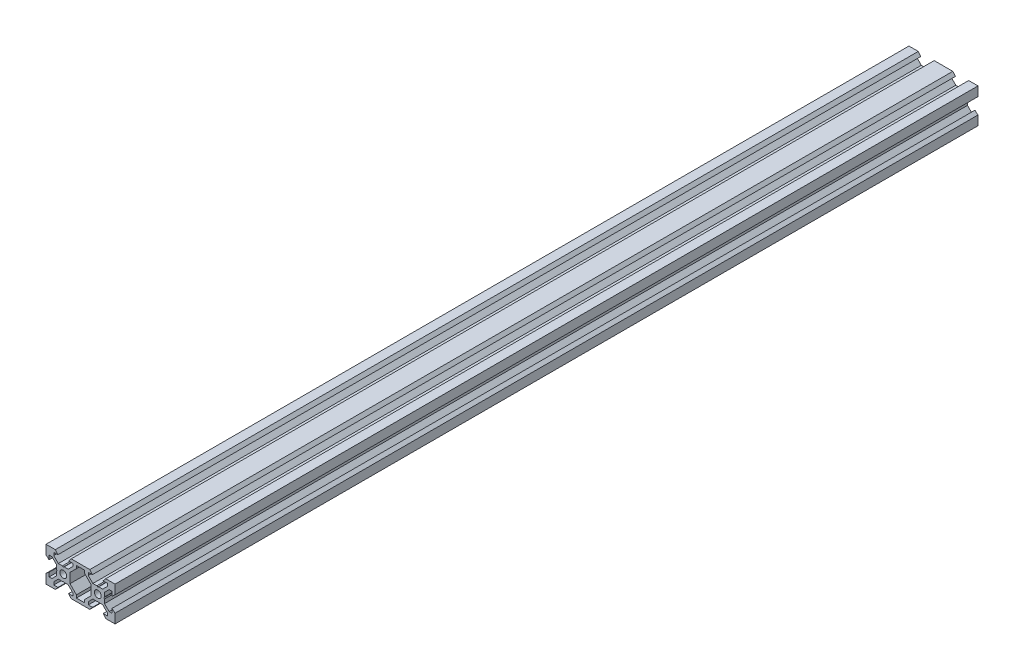
SolidWorks part; units mm, degrees
ref_plane "Front Plane" through (0, 0, 0) normal (0, 0, 1) x (1, 0, 0)
ref_plane "Top Plane" through (0, 0, 0) normal (0, 1, 0) x (1, 0, 0)
ref_plane "Right Plane" through (0, 0, 0) normal (1, 0, 0) x (0, 0, -1)
sketch "Sketch1" plane through (0, 0, 0) normal (0, 0, 1) x (1, 0, 0)
  line L0 (-5.3896, 10) -> (5.3896, 10)
  line L1 (0, 10) -> (0, 4.6104) construction
  line L2 (-6.1, -2.8393) -> (-2.3769, -6.5562)
  line L3 (5.3896, -10) -> (-5.3896, -10) construction
  line L5 (-6.1, 2.8393) -> (-6.1, -2.8393)
  line L6 (-4.5, 8.2) -> (-4.5, 6.5562)
  line L7 (2.3832, 6.5562) -> (2.3832, 8.2)
  line L9 (-6.1, 2.8393) -> (-2.3832, 6.5562)
  line L10 (-4.5, 6.5562) -> (-7.1607, 3.9)
  line L11 (-2.3832, 6.5562) -> (-2.3832, 8.2)
  line L12 (-5.3896, 10) -> (-6.9, 8.2)
  line L13 (6.1, 2.8393) -> (2.3832, 6.5562)
  line L14 (-6.9, 8.2) -> (-4.5, 8.2)
  line L15 (-16.5562, 5.5) -> (-18.2, 5.5)
  line L16 (0, 0) -> (6.1, 0) construction
  line L17 (-6.9, -8.2) -> (-4.5, -8.2)
  line L18 (-2.3769, -6.5562) -> (-2.3769, -8.2)
  line L19 (-5.3896, -10) -> (-6.9, -8.2)
  line L20 (2.3769, -6.5562) -> (2.3769, -8.2)
  line L21 (-9.4804, -3.9002) -> (-10, -3.6002)
  line L22 (-9.4804, 3.8998) -> (-10, 3.5998)
  line L23 (6.1, -2.8393) -> (2.3769, -6.5562)
  line L24 (-2.3769, -8.2) -> (2.3769, -8.2)
  line L25 (-2.3832, 8.2) -> (2.3832, 8.2)
  line L26 (-9.4804, 3.8998) -> (-7.1607, 3.9)
  line L27 (-5.3896, -10) -> (5.3896, -10)
  line L28 (-9.4804, -3.9002) -> (-7.1604, -3.9002)
  line L29 (-4.5, -6.5562) -> (-7.1607, -3.9)
  line L30 (-20, 10) -> (20, 10) construction
  line L32 (6.1, 2.8393) -> (6.1, -2.8393)
  line L33 (-4.5, -8.2) -> (-4.5, -6.5562)
  line L34 (-16.5562, -5.5) -> (-18.2, -5.5)
  line L36 (-10, 0) -> (-10, 8.2) construction
  line L37 (-20, -10) -> (-14.6104, -10) construction
  line L38 (-20, -10) -> (-20, -4.6104) construction
  line L39 (-20, 10) -> (-20, 4.6104) construction
  line L40 (-20, 10) -> (-14.6104, 10) construction
  line L41 (-20, -10) -> (-20, -4.6104)
  line L42 (-15.5, -8.2) -> (-15.5, -6.5562)
  line L43 (-20, -10) -> (-14.6104, -10)
  line L44 (7.1519, 3.8998) -> (9.4804, 3.8998)
  line L45 (-16.5562, -5.5) -> (-13.9, -2.8393)
  line L46 (-15.5, -6.5562) -> (-12.8393, -3.9)
  line L47 (-12.8393, -3.9) -> (-10.5196, -3.9002)
  line L48 (-13.9, -2.8393) -> (-13.9, -0.5196)
  line L49 (-12.8393, 3.9) -> (-10.5196, 3.8998)
  line L50 (-13.9, 0.5196) -> (-13.9, 2.8393)
  line L51 (-13.9, 0.5196) -> (-13.6, 0)
  line L52 (-13.6, 0) -> (-13.9, -0.5196)
  line L53 (-10.5196, 3.8998) -> (-10, 3.5998)
  line L54 (-10.5196, -3.9002) -> (-10, -3.6002)
  line L55 (-20, -4.6104) -> (-18.2, -3.1)
  line L56 (-14.6104, -10) -> (-13.1, -8.2)
  line L57 (-18.2, -3.1) -> (-18.2, -5.5)
  line L58 (-13.1, -8.2) -> (-15.5, -8.2)
  line L59 (-20, -10) -> (20, -10) construction
  line L60 (-20, -10) -> (-20, 10) construction
  line L61 (-13.1, 8.2) -> (-15.5, 8.2)
  line L62 (-18.2, 3.1) -> (-18.2, 5.5)
  line L63 (-14.6104, 10) -> (-13.1, 8.2)
  line L64 (-20, 4.6104) -> (-18.2, 3.1)
  line L65 (-15.5, 6.5562) -> (-12.8393, 3.9)
  line L66 (-16.5562, 5.5) -> (-13.9, 2.8393)
  line L67 (-20, 10) -> (-20, 4.6104)
  line L68 (-20, 10) -> (-14.6104, 10)
  line L69 (-15.5, 8.2) -> (-15.5, 6.5562)
  line L70 (4.5, 6.5562) -> (7.1519, 3.8998)
  line L71 (15.5, 6.5562) -> (12.8481, 3.8998)
  line L72 (0, -10) -> (0, 10) construction
  line L73 (-20, -10) -> (0, 10) construction
  line L74 (10.5196, 3.8998) -> (12.8481, 3.8998)
  line L75 (12.8393, -3.9) -> (10.5192, -3.9)
  line L76 (20, -10) -> (0, 10) construction
  line L77 (20, -10) -> (20, 10) construction
  line L78 (20, 10) -> (14.6104, 10) construction
  line L79 (20, 10) -> (20, 4.6104) construction
  line L80 (20, -10) -> (20, -4.6104) construction
  line L81 (20, -10) -> (14.6104, -10) construction
  line L82 (10, 0) -> (10, 8.2) construction
  line L83 (20, 10) -> (20, 4.6104)
  line L84 (15.5, 8.2) -> (15.5, 6.5562)
  line L85 (20, 10) -> (14.6104, 10)
  line L87 (16.5562, 5.5) -> (13.9, 2.8393)
  line L89 (20, 4.6104) -> (18.2, 3.1)
  line L90 (14.6104, 10) -> (13.1, 8.2)
  line L91 (18.2, 3.1) -> (18.2, 5.5)
  line L92 (13.1, 8.2) -> (15.5, 8.2)
  line L93 (13.1, -8.2) -> (15.5, -8.2)
  line L94 (18.2, -3.1) -> (18.2, -5.5)
  line L95 (14.6104, -10) -> (13.1, -8.2)
  line L96 (20, -4.6104) -> (18.2, -3.1)
  line L97 (10.5196, -3.9002) -> (10, -3.6002)
  line L98 (10.5196, 3.8998) -> (10, 3.5998)
  line L99 (13.6, 0) -> (13.9, -0.5196)
  line L100 (13.9, 0.5196) -> (13.6, 0)
  line L101 (13.9, 0.5196) -> (13.9, 2.8393)
  line L102 (9.4808, -3.9) -> (7.1607, -3.9)
  line L103 (13.9, -2.8393) -> (13.9, -0.5196)
  line L105 (15.5, -6.5562) -> (12.8393, -3.9)
  line L106 (16.5562, -5.5) -> (13.9, -2.8393)
  line L107 (20, -10) -> (20, -4.6104)
  line L108 (20, -10) -> (14.6104, -10)
  line L109 (15.5, -8.2) -> (15.5, -6.5562)
  line L111 (16.5562, -5.5) -> (18.2, -5.5)
  line L112 (4.5, -8.2) -> (4.5, -6.5562)
  line L114 (4.5, -6.5562) -> (7.1607, -3.9)
  line L121 (9.4804, 3.8998) -> (10, 3.5998)
  line L122 (9.4804, -3.9002) -> (10, -3.6002)
  line L124 (5.3896, -10) -> (6.9, -8.2)
  line L126 (6.9, -8.2) -> (4.5, -8.2)
  line L128 (16.5562, 5.5) -> (18.2, 5.5)
  line L129 (6.9, 8.2) -> (4.5, 8.2)
  line L131 (5.3896, 10) -> (6.9, 8.2)
  line L135 (4.5, 8.2) -> (4.5, 6.5562)
  circle A0 centre (-10, 0) radius 2
  circle A1 centre (10, 0) radius 2
  point P104 (7.1519, 0)
  point P106 (6.1, 0)
  dimension "D14" = 4
  dimension "D1" = 20
  dimension "D2" = 5.3896
  dimension "D3" = 1.8
  dimension "D4" = 1.5104
  dimension "D5" = 4.5
  dimension "D6" = 5.5
  dimension "D7" = 120
  dimension "D8" = 0.3
  dimension "D9" = 2.3197
  dimension "D10" = 7.8
  dimension "D11" = 20
  dimension "D12" = 1.5
  dimension "D13" = 2.6607
  dimension "D15" = 50
  dimension "D16" = 1.5
  dimension "D17" = 1.8
  dimension "D18" = 16.4
  dimension "D19" = 2.3832
  dimension "D20" = 45
extrude "Boss-Extrude1" add sketch "Sketch1" along normal blind 500
